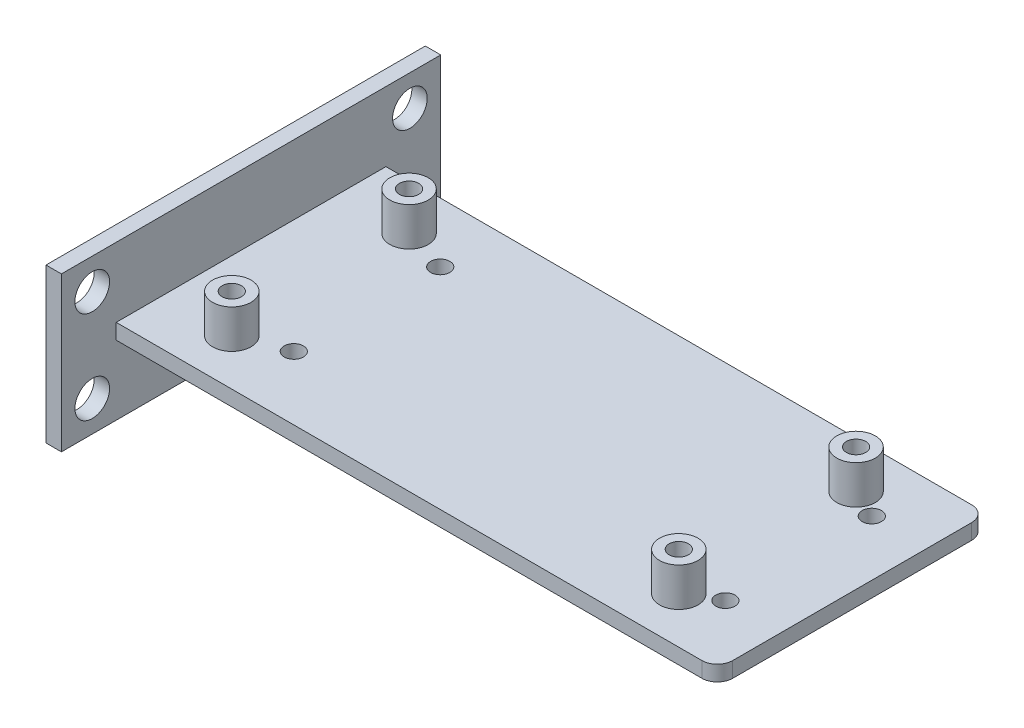
SolidWorks part; units mm, degrees
material "ABS"
ref_plane "Спереди" through (0, 0, 0) normal (0, 0, 1) x (1, 0, 0)
ref_plane "Сверху" through (0, 0, 0) normal (0, 1, 0) x (1, 0, 0)
ref_plane "Справа" through (0, 0, 0) normal (1, 0, 0) x (0, 0, -1)
sketch "Эскиз1" plane through (0, 0, 0) normal (0, 1, 0) x (1, 0, 0)
  line L1 (0, 0) -> (80, 0)
  line L2 (0, 0) -> (0, -35)
  line L3 (0, -35) -> (80, -35)
  line L4 (80, 0) -> (80, -35)
  dimension "D1" = 80
  dimension "D2" = 35
extrude "Бобышка-Вытянуть1" add sketch "Эскиз1" along normal blind 2
sketch "Эскиз2" plane through (0, 2, 0) normal (0, 1, 0) x (1, 0, 0)
  line L0 (0, 0) -> (0, -35) construction
  line L1 (80, -35) -> (80, 0) construction
  line L2 (80, 0) -> (0, 0) construction
  line L3 (0, -35) -> (80, -35) construction
  circle A0 centre (11, -6) radius 2.5
  circle A1 centre (11, -29) radius 2.5
  circle A2 centre (69, -6) radius 2.5
  circle A3 centre (69, -29) radius 2.5
  dimension "D1" = 11
  dimension "D2" = 11
  dimension "D3" = 11
  dimension "D4" = 11
  dimension "D5" = 6
  dimension "D6" = 6
  dimension "D7" = 5
  dimension "D8" = 6
  dimension "D9" = 6
  dimension "D10" = 5
  dimension "D11" = 5
  dimension "D12" = 5
extrude "Бобышка-Вытянуть2" add sketch "Эскиз2" along normal blind 5
sketch "Эскиз3" plane through (0, 7, 0) normal (0, 1, 0) x (1, 0, 0)
  circle A0 centre (11, -6) radius 1.25
  circle A1 centre (11, -29) radius 1.25
  circle A2 centre (69, -6) radius 1.25
  circle A3 centre (69, -29) radius 1.25
  dimension "D1" = 2.5
  dimension "D2" = 2.5
  dimension "D3" = 2.5
  dimension "D4" = 2.5
extrude "Вырез-Вытянуть1" cut sketch "Эскиз3" against normal through all both and the other way through all
sketch "Эскиз4" plane through (0, 2, 0) normal (0, 1, 0) x (1, 0, 0)
  line L0 (0, -17.5) -> (80, -17.5) construction
  line L1 (0, 0) -> (0, -35) construction
  line L2 (80, -35) -> (80, 0) construction
  circle A0 centre (4, -17.5) radius 2
  circle A1 centre (76, -17.5) radius 2
  dimension "D2" = 4
  dimension "D3" = 4
  dimension "D4" = 4
  dimension "D1" = 4
extrude "Вырез-Вытянуть2" [suppressed] cut sketch "Эскиз4" against normal through all
fillet "Скругление1" radius 2 1 edges at (0, 1, 0)
fillet "Скругление2" radius 2 1 edges at (0, 1, 35)
fillet "Скругление3" radius 2 1 edges at (80, 1, 35)
fillet "Скругление4" radius 2 1 edges at (80, 1, 0)
sketch "Эскиз5" plane through (0, 0, 0) normal (0, -1, 0) x (1, 0, 0)
  circle A0 centre (16.7893, 26.746) radius 1.25
  circle A1 centre (72.7893, 26.746) radius 1.25
  circle A2 centre (72.7893, 7.746) radius 1.25
  circle A3 centre (16.7893, 7.746) radius 1.25
  dimension "D1" = 2
  dimension "D2" = 2
extrude "Вырез-Вытянуть3" cut sketch "Эскиз5" against normal blind 10
sketch "Эскиз6" plane through (0, 0, 0) normal (0, -1, 0) x (1, 0, 0)
  circle A0 centre (16.7893, 26.746) radius 1.25
  circle A1 centre (16.7893, 26.746) radius 2.5
  circle A2 centre (72.7893, 26.746) radius 2.5
  circle A3 centre (72.7893, 26.746) radius 1.25
  circle A4 centre (72.7893, 7.746) radius 2.5
  circle A5 centre (72.7893, 7.746) radius 1.25
  circle A6 centre (16.7893, 7.746) radius 2.5
  circle A7 centre (16.7893, 7.746) radius 1.25
  dimension "D1" = 2
  dimension "D2" = 2
extrude "Бобышка-Вытянуть3" add sketch "Эскиз6" along normal blind 4
sketch "Эскиз7" plane through (0, 0, 0) normal (-1, 0, 0) x (0, 0, 1)
  line L0 (17.5, 2) -> (17.5, 0) construction
  line L1 (2, 2) -> (33, 2) construction
  line L2 (2, 0) -> (33, 0) construction
  line L3 (-7.1094, 1) -> (42.7824, 1) construction
  line L4 (42.1094, -9) -> (-7.1094, -9)
  line L5 (42.1094, -9) -> (42.1094, 11)
  line L6 (42.1094, 11) -> (-7.1094, 11)
  line L7 (-7.1094, -9) -> (-7.1094, 11)
  line L8 (42.1094, -9) -> (-7.1094, 11) construction
  line L9 (42.1094, 11) -> (-7.1094, -9) construction
  circle A0 centre (38.1094, -5) radius 2.25
  circle A1 centre (-3.1094, -5) radius 2.25
  circle A2 centre (-3.1094, 7) radius 2.25
  circle A3 centre (38.1094, 7) radius 2.25
  point P6 (17.5, 1)
  dimension "D1" = 4
  dimension "D2" = 4
  dimension "D3" = 20
extrude "Бобышка-Вытянуть4" add sketch "Эскиз7" against normal blind 2
